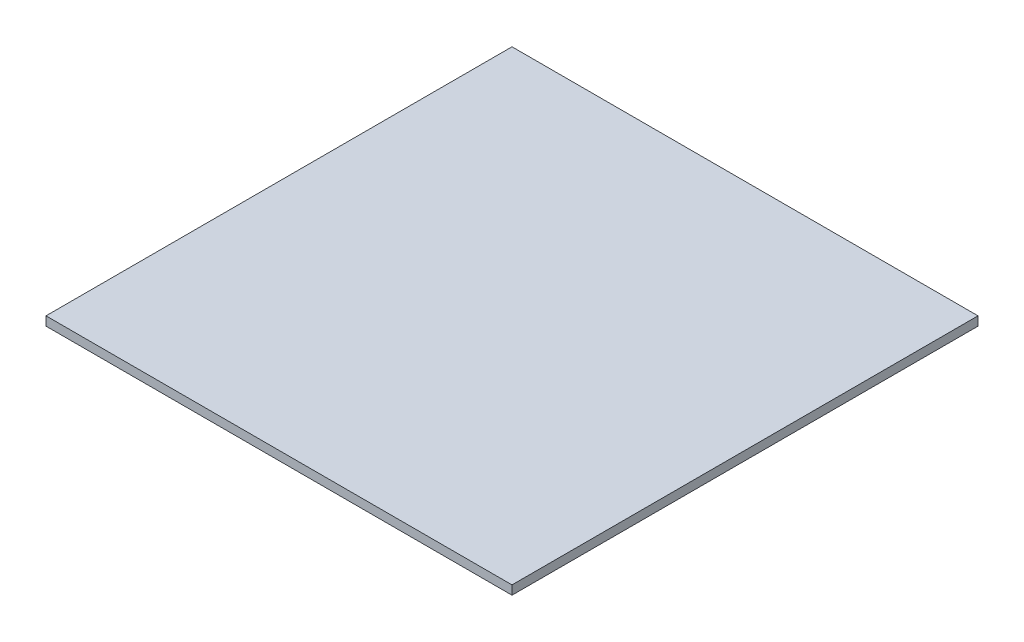
SolidWorks part; units mm, degrees
ref_plane "Front Plane" through (0, 0, 0) normal (0, 0, 1) x (1, 0, 0)
ref_plane "Top Plane" through (0, 0, 0) normal (0, 1, 0) x (1, 0, 0)
ref_plane "Right Plane" through (0, 0, 0) normal (1, 0, 0) x (0, 0, -1)
sketch "Sketch2" plane through (0, 0, 0) normal (0, 1, 0) x (1, 0, 0)
  line L1 (-65, -65) -> (65, -65)
  line L2 (-65, -65) -> (-65, 65)
  line L3 (-65, 65) -> (65, 65)
  line L4 (65, -65) -> (65, 65)
  line L5 (-65, -65) -> (65, 65) construction
  line L6 (-65, 65) -> (65, -65) construction
  point P0 (0, 0)
  dimension "D1" = 130
  dimension "D2" = 130
extrude "Boss-Extrude1" add sketch "Sketch2" along normal blind 2.5
